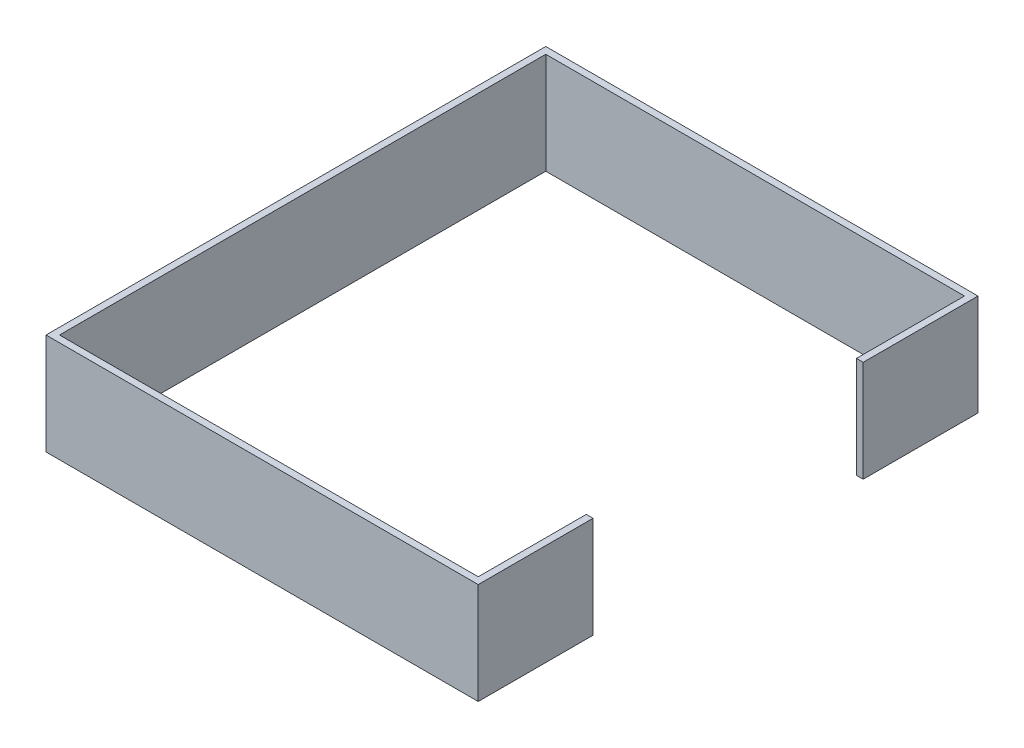
SolidWorks part; units mm, degrees
ref_plane "Front Plane" through (0, 0, 0) normal (0, 0, 1) x (1, 0, 0)
ref_plane "Top Plane" through (0, 0, 0) normal (0, 1, 0) x (1, 0, 0)
ref_plane "Right Plane" through (0, 0, 0) normal (1, 0, 0) x (0, 0, -1)
sketch "Sketch1" plane through (0, 0, 0) normal (1, 0, 0) x (0, 0, -1)
  line L1 (-236.0056, 1148.5961) -> (503.9944, 1148.5961)
  line L2 (-236.0056, 1148.5961) -> (-236.0056, 1298.5961)
  line L3 (-236.0056, 1298.5961) -> (503.9944, 1298.5961)
  line L4 (503.9944, 1148.5961) -> (503.9944, 1298.5961)
  dimension "D1" = 740
  dimension "D2" = 150
extrude "Boss-Extrude1" add sketch "Sketch1" along normal up to surface (441.9431 mm away) and the other way up to surface (198.0569 mm away)
sketch "Sketch2" plane through (0, 1298.5961, 0) normal (0, 1, 0) x (1, 0, 0)
  line L1 (431.9431, -226.0056) -> (-188.0569, -226.0056)
  line L2 (431.9431, -226.0056) -> (431.9431, 493.9944)
  line L3 (431.9431, 493.9944) -> (-188.0569, 493.9944)
  line L4 (-188.0569, -226.0056) -> (-188.0569, 493.9944)
  line L5 (431.9431, -226.0056) -> (-188.0569, 493.9944) construction
  line L6 (431.9431, 493.9944) -> (-188.0569, -226.0056) construction
  point P0 (121.9431, 133.9944)
  dimension "D1" = 620
  dimension "D2" = 720
extrude "Cut-Extrude1" cut sketch "Sketch2" against normal up to surface (150 mm away) up to face at (121.9431, 1148.5961, -133.9944)
sketch "Sketch3" plane through (441.9431, 0, 0) normal (1, 0, 0) x (0, 0, -1)
  line L0 (133.9944, 1148.5961) -> (333.9944, 1148.5961)
  line L1 (503.9944, 1148.5961) -> (-236.0056, 1148.5961) construction
  line L2 (333.9944, 1148.5961) -> (333.9944, 1298.5961)
  line L3 (-236.0056, 1298.5961) -> (503.9944, 1298.5961) construction
  line L4 (333.9944, 1298.5961) -> (-66.0056, 1298.5961)
  line L5 (-66.0056, 1298.5961) -> (-66.0056, 1148.5961)
  line L6 (-66.0056, 1148.5961) -> (133.9944, 1148.5961)
  dimension "D1" = 400
extrude "Cut-Extrude2" cut sketch "Sketch3" against normal up to surface (630 mm away) up to face at (-188.0569, 1223.5961, -133.9944)
